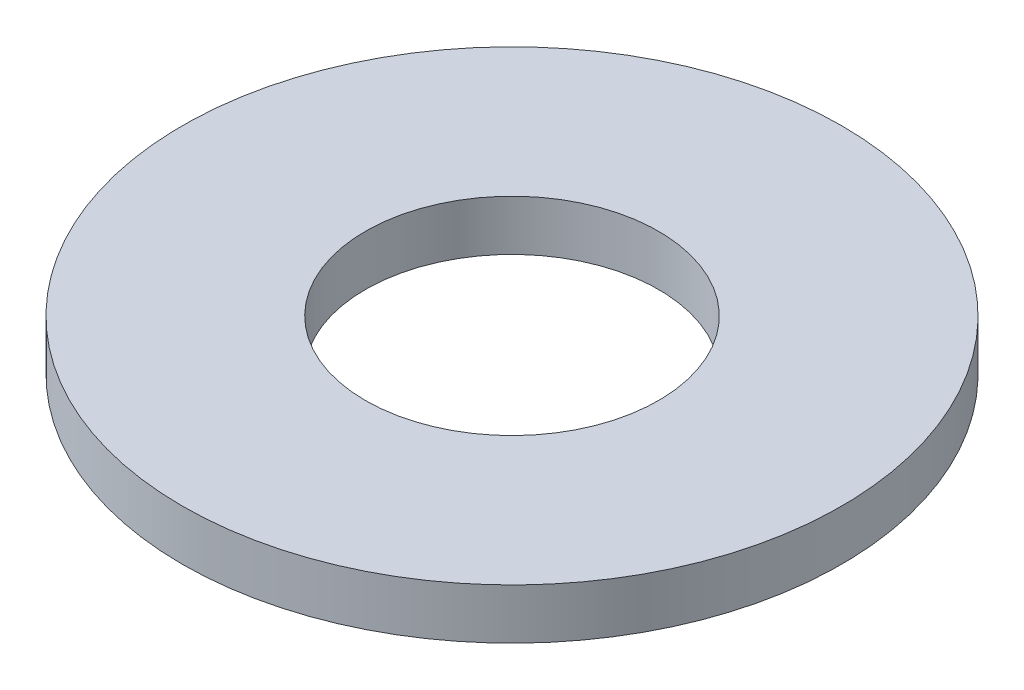
SolidWorks part; units mm, degrees
ref_plane "Front Plane" through (0, 0, 0) normal (0, 0, 1) x (1, 0, 0)
ref_plane "Top Plane" through (0, 0, 0) normal (0, 1, 0) x (1, 0, 0)
ref_plane "Right Plane" through (0, 0, 0) normal (1, 0, 0) x (0, 0, -1)
sketch "Sketch1" plane through (0, 0, 0) normal (0, 1, 0) x (1, 0, 0)
  circle A0 centre (0, 0) radius 7.1374
  dimension "OD" = 14.2748
extrude "Boss-Extrude1" add sketch "Sketch1" along normal blind 1.0922
sketch "Sketch5" plane through (0, 1.0922, 0) normal (0, 1, 0) x (-1, 0, 0)
  circle A0 centre (0, 0) radius 3.175
  dimension "ID" = 6.35
extrude "Cut-Extrude1" cut sketch "Sketch5" against normal through all
